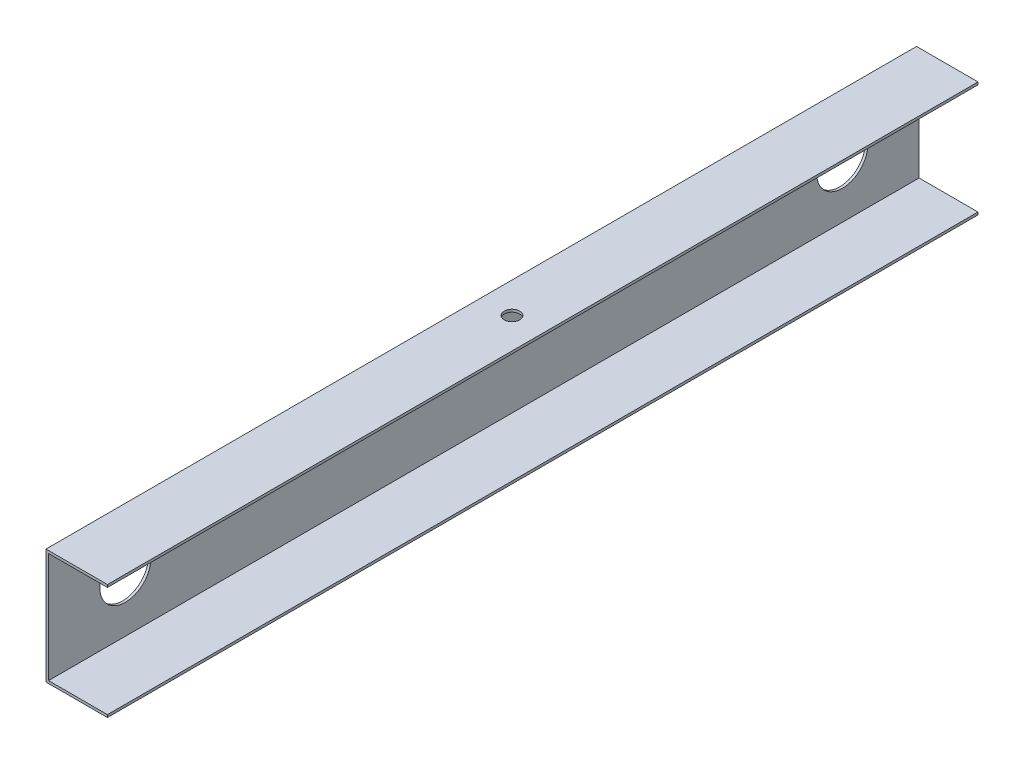
SolidWorks part; units mm, degrees
ref_plane "Front Plane" through (0, 0, 0) normal (0, 0, 1) x (1, 0, 0)
ref_plane "Top Plane" through (0, 0, 0) normal (0, 1, 0) x (1, 0, 0)
ref_plane "Right Plane" through (0, 0, 0) normal (1, 0, 0) x (0, 0, -1)
sketch "Sketch2" plane through (0, 0, 0) normal (0, 0, 1) x (1, 0, 0)
  line L0 (0, 0) -> (24, 0)
  line L1 (0, 0) -> (0, -45)
  line L2 (0, -45) -> (24, -45)
  line L3 (1, -44) -> (24, -44)
  line L4 (1, -1) -> (1, -44)
  line L5 (1, -1) -> (24, -1)
  line L6 (24, -44) -> (24, -45)
  line L7 (24, 0) -> (24, -1)
  dimension "D1" = 1
  dimension "D2" = 45
extrude "Boss-Extrude1" add sketch "Sketch2" along normal blind 340
sketch "Sketch3" plane through (0, 0, 0) normal (-1, 0, 0) x (0, 0, 1)
  line L2 (170, 0) -> (170, -45) construction
  line L3 (340, 0) -> (0, 0) construction
  line L4 (340, -45) -> (0, -45) construction
  circle A0 centre (30, -22.5) radius 10
  circle A1 centre (310, -22.5) radius 10
extrude "Cut-Extrude1" cut sketch "Sketch3" against normal blind 340
sketch "Sketch4" plane through (0, 0, 0) normal (0, 1, 0) x (1, 0, 0)
  line L0 (0, -170) -> (24, -170) construction
  line L1 (0, -340) -> (0, 0) construction
  line L2 (24, -340) -> (24, 0) construction
  circle A0 centre (12, -170) radius 3
  dimension "D1" = 12
  dimension "D2" = 6
extrude "Cut-Extrude2" cut sketch "Sketch4" against normal blind 25
